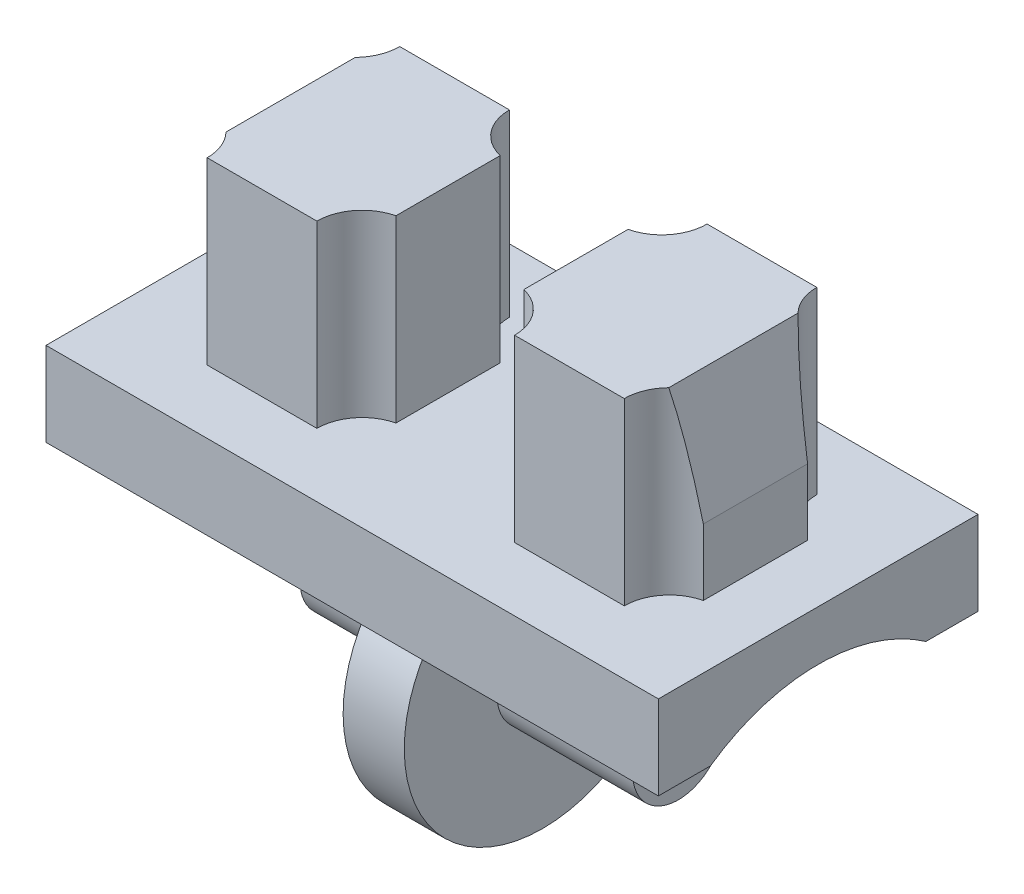
SolidWorks part; units mm, degrees
ref_plane "Ön Düzlem" through (0, 0, 0) normal (0, 0, 1) x (1, 0, 0)
ref_plane "Üst Düzlem" through (0, 0, 0) normal (0, 1, 0) x (1, 0, 0)
ref_plane "Sağ Düzlem" through (0, 0, 0) normal (1, 0, 0) x (0, 0, -1)
sketch "Çizim3" plane through (0, 0, 0) normal (0, 1, 0) x (1, 0, 0)
  line L1 (0, 0) -> (-15.52, 0)
  line L2 (0, 0) -> (0, -8.1)
  line L3 (0, -8.1) -> (-15.52, -8.1)
  line L4 (-15.52, 0) -> (-15.52, -8.1)
  dimension "D1" = 15.52
  dimension "D2" = 8.1
extrude "Yükseklik-Ekstrüzyon1" add sketch "Çizim3" against normal blind 2.13
sketch "Çizim4" plane through (0, 0, 0) normal (0, 1, 0) x (1, 0, 0)
  line L0 (-15.52, 0) -> (-15.52, -8.1) construction
  line L1 (-13.045, -1.61) -> (-10.265, -1.61)
  line L2 (-13.93, -2.7291) -> (-13.93, -5.3709)
  line L3 (-13.045, -6.49) -> (-10.265, -6.49)
  line L4 (-9.38, -2.7291) -> (-9.38, -5.3709)
  line L10 (-15.52, -8.1) -> (0, -8.1) construction
  line L11 (-11.655, -1.61) -> (-11.655, -6.49) construction
  line L12 (-9.38, -4.05) -> (-13.93, -4.05) construction
  line L13 (-7.76, 0) -> (-7.76, -8.1) construction
  line L14 (0, 0) -> (-15.52, 0) construction
  line L15 (-6.14, -2.7291) -> (-6.14, -5.3709)
  line L16 (-2.475, -6.49) -> (-5.255, -6.49)
  line L17 (-1.59, -2.7291) -> (-1.59, -5.3709)
  line L18 (-2.475, -1.61) -> (-5.255, -1.61)
  arc A0 (-10.265, -6.49) -> (-9.38, -5.3709) centre (-9.115, -6.49) cw
  arc A1 (-13.045, -6.49) -> (-13.93, -5.3709) centre (-14.195, -6.49) ccw
  arc A2 (-10.265, -1.61) -> (-9.38, -2.7291) centre (-9.115, -1.61) ccw
  arc A3 (-13.045, -1.61) -> (-13.93, -2.7291) centre (-14.195, -1.61) cw
  arc A4 (-5.255, -6.49) -> (-6.14, -5.3709) centre (-6.405, -6.49) ccw
  arc A5 (-2.475, -6.49) -> (-1.59, -5.3709) centre (-1.325, -6.49) cw
  arc A6 (-2.475, -1.61) -> (-1.59, -2.7291) centre (-1.325, -1.61) ccw
  arc A7 (-5.255, -1.61) -> (-6.14, -2.7291) centre (-6.405, -1.61) cw
  point P23 (-11.655, -4.05)
  dimension "D9" = 1.15
  dimension "D10" = 2.54
  dimension "D1" = 1.59
  dimension "D3" = 1.61
  dimension "D5" = 4.88
  dimension "D6" = 4.55
  dimension "D11" = 0
extrude "Yükseklik-Ekstrüzyon2" add sketch "Çizim4" along normal blind 4.55
ref_plane "Düzlem1" through (0, 0, 5.3709) normal (0, 0, 1) x (1, 0, 0)
sketch "Çizim6" plane through (0, 0, 5.3709) normal (0, 0, 1) x (1, 0, 0)
  line L0 (-1.59, 0) -> (-1.59, 1.68)
  line L1 (-1.59, 4.55) -> (-1.59, 0) construction
  line L2 (-1.59, 1.68) -> (-2.475, 1.68)
  line L3 (-2.475, 4.55) -> (-2.475, 0) construction
  line L4 (-1.59, 1.68) -> (-1.59, 4.55)
  line L5 (-1.59, 4.55) -> (-2.1489, 4.55)
  line L6 (-1.59, 1.68) -> (-2.1489, 4.55)
  dimension "D1" = 1.68
  dimension "D2" = 11.02
extrude "Kes-Ekstrüzyon2" cut sketch "Çizim6" against normal mid plane 24.55 contours L4 L5 L6
sketch "Çizim7" plane through (0, 0, 5.3709) normal (0, 0, 1) x (1, 0, 0)
  line L0 (-13.93, 0) -> (-13.93, 1.68)
  line L1 (-13.93, 4.55) -> (-13.93, 0) construction
  line L2 (-13.93, 1.68) -> (-13.045, 1.68)
  line L3 (-13.045, 4.55) -> (-13.045, 0) construction
  line L6 (-13.93, 1.68) -> (-13.3711, 4.55)
  line L7 (-13.045, 4.55) -> (-13.93, 4.55) construction
  line L8 (-13.93, 1.68) -> (-13.93, 4.55)
  line L9 (-13.93, 4.55) -> (-13.3711, 4.55)
  dimension "D1" = 1.68
  dimension "D2" = 11.02
extrude "Kes-Ekstrüzyon3" cut sketch "Çizim7" against normal mid plane 24.55 contours L9 L8 L6
sketch "Çizim8" plane through (0, 0, 0) normal (1, 0, 0) x (0, 0, -1)
  line L0 (-4.05, 0) -> (-4.05, -4.86) construction
  line L1 (-8.1, 0) -> (0, 0) construction
  line L3 (-6.78, -2.6618) -> (-6.78, -2.13)
  line L4 (-8.1, -2.13) -> (0, -2.13) construction
  line L5 (-1.32, -2.6618) -> (-1.32, -2.13)
  line L6 (-6.78, -2.6618) -> (-1.32, -2.6618) construction
  line L7 (-6.78, -2.13) -> (-1.32, -2.13)
  circle A0 centre (-4.05, -4.86) radius 1.155
  arc A1 (-6.78, -2.6618) -> (-1.32, -2.6618) centre (-4.05, -4.86) ccw
  arc A3 (-6.78, -2.13) -> (-1.32, -2.13) centre (-4.05, -6.0171) cw
  dimension "D2" = 2.31
  dimension "D3" = 7.01
  dimension "D5" = 4.75
  dimension "D1" = 4.86
  dimension "D4" = 5.46
extrude "Kes-Ekstrüzyon4" cut sketch "Çizim8" against normal through all contours A3 L7
ref_plane "Düzlem2" through (-7.76, 0, 0) normal (1, 0, 0) x (0, 0, -1)
sketch "Çizim10" plane through (-7.76, 0, 0) normal (1, 0, 0) x (0, 0, -1)
  line L0 (-6.78, -2.6618) -> (-1.32, -2.6618) construction
  line L1 (-4.05, -4.86) -> (-4.05, -1.355) construction
  line L2 (-6.78, -2.6618) -> (-6.78, -2.13)
  line L3 (-1.32, -2.6618) -> (-1.32, -2.13)
  circle A0 centre (-4.05, -4.86) radius 1.155
  circle A1 centre (-4.05, -4.86) radius 3.505
  arc A2 (-6.78, -2.13) -> (-1.32, -2.13) centre (-4.05, -6.0171) cw
  dimension "D1" = 7.01
  dimension "D2" = 2.31
  dimension "D3" = 4.75
extrude "Yükseklik-Ekstrüzyon4" add sketch "Çizim10" along normal mid plane 1.55 contours A2 L2 A1 L3 | A1 A0
sketch "Çizim11" plane through (-7.76, 0, 0) normal (1, 0, 0) x (0, 0, -1)
  circle A0 centre (-4.05, -4.86) radius 1.155
  dimension "D1" = 2.31
extrude "Yükseklik-Ekstrüzyon5" add sketch "Çizim11" along normal mid plane 8.43
